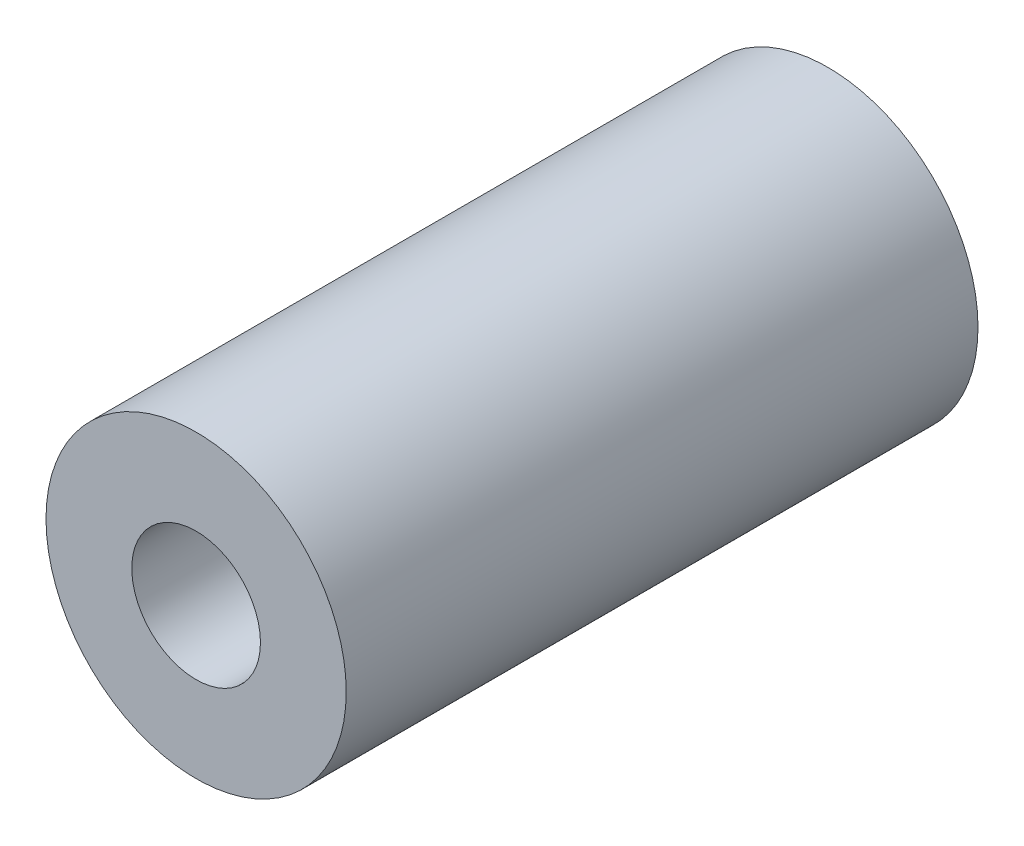
SolidWorks part; units mm, degrees
ref_plane "Front Plane" through (0, 0, 0) normal (0, 0, 1) x (1, 0, 0)
ref_plane "Top Plane" through (0, 0, 0) normal (0, 1, 0) x (1, 0, 0)
ref_plane "Right Plane" through (0, 0, 0) normal (1, 0, 0) x (0, 0, -1)
sketch "Sketch1" plane through (0, 0, 0) normal (1, 0, 0) x (0, 0, -1)
  line L0 (0, 0) -> (12.8971, 0) construction
  line L1 (0, 8.6765) -> (0, -1.0882) construction
  line L2 (0, 3.5) -> (14.73, 3.5)
  line L3 (0, 3.5) -> (0, 1.5)
  line L4 (0, 1.5) -> (14.73, 1.5)
  line L5 (14.73, 3.5) -> (14.73, 1.5)
  dimension "D1" = 3
  dimension "D2" = 7
  dimension "D3" = 14.73
revolve "Revolve1" add sketch "Sketch1" angle 360 about L0
